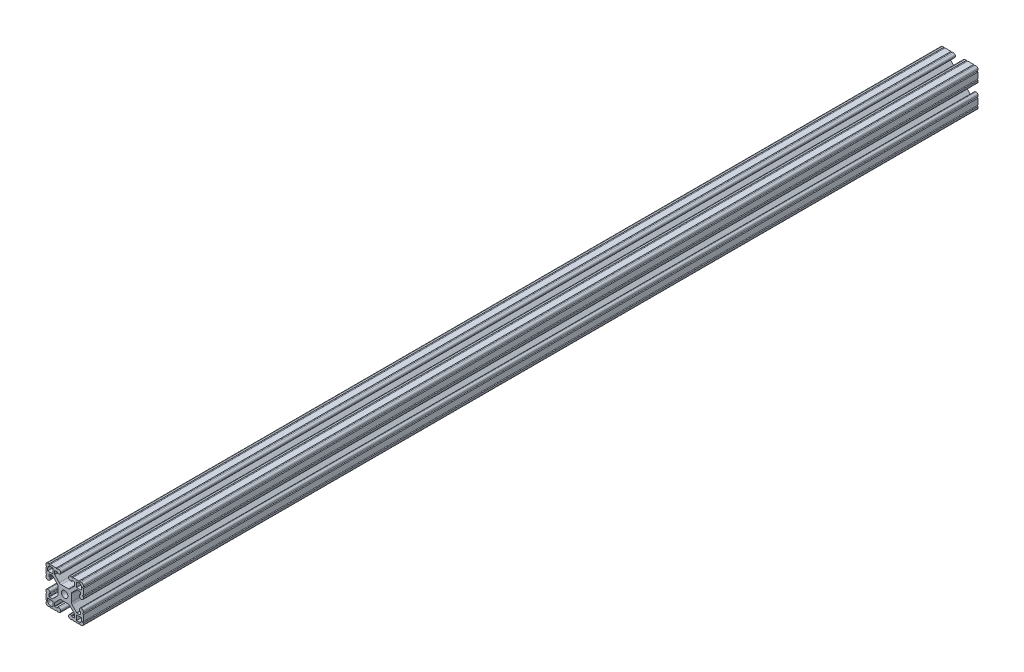
SolidWorks part; units mm, degrees
ref_plane "Front Plane" through (0, 0, 0) normal (0, 0, 1) x (1, 0, 0)
ref_plane "Top Plane" through (0, 0, 0) normal (0, 1, 0) x (1, 0, 0)
ref_plane "Right Plane" through (0, 0, 0) normal (1, 0, 0) x (0, 0, -1)
sketch "Sketch1" plane through (0, 0, 0) normal (0, 0, 1) x (1, 0, 0)
  line L0 (0, -19.05) -> (0, 19.05) construction
  line L1 (19.05, 0) -> (-19.05, 0) construction
  line L2 (4.064, 19.05) -> (-4.064, 19.05) construction
  line L3 (0, -6.7564) -> (0, 6.7564) construction
  line L4 (-4.064, 19.05) -> (-4.064, 14.986) construction
  line L5 (19.05, -10.287) -> (19.05, 10.287) construction
  line L6 (0, -3.3274) -> (0, 3.3274) construction
  line L7 (0, 0) -> (-19.05, 19.05) construction
  line L8 (-8.4474, 10.6026) -> (-10.6026, 8.4474) construction
  point P4 (0, 0)
  point P8 (0, 0)
  point P11 (0, 19.05)
  point P14 (0, 0)
  point P18 (19.05, 0)
  point P21 (0, 0)
  point P24 (-9.525, 9.525)
  point P26 (-9.525, 9.525)
  dimension "T-Slot Width" = 8.128
  dimension "Thickness" = 4.064
  dimension "Opening Width" = 20.574
  dimension "Slot Depth" = 12.2936
  dimension "Center Hole Diameter" = 6.6548
  dimension "Rail Height" = 38.1
  dimension "Rail Width" = 38.1
  dimension "D1" = 45
  dimension "Wall" = 3.048
sketch "Sketch2" plane through (0, 0, 0) normal (1, 0, 0) x (0, 0, -1)
  line L0 (-457.2, 0) -> (457.2, 0) construction
  line L1 (-381, -19.05) -> (-381, 19.05) construction
  line L2 (381, -19.05) -> (381, 19.05) construction
  line L3 (0, -19.05) -> (0, 19.05) construction
  point P4 (0, 0)
  point P7 (-381, 0)
  point P10 (381, 0)
  dimension "Length" = 914.4
  dimension "D1" = 76.2
  dimension "D2" = 76.2
sketch "Sketch3" plane through (0, 0, 0) normal (0, 0, 1) x (1, 0, 0)
  line L1 (19.05, -19.05) -> (-19.05, -19.05)
  line L2 (19.05, -19.05) -> (19.05, 19.05)
  line L3 (19.05, 19.05) -> (-19.05, 19.05)
  line L4 (-19.05, -19.05) -> (-19.05, 19.05)
  line L5 (19.05, -19.05) -> (-19.05, 19.05) construction
  line L6 (19.05, 19.05) -> (-19.05, -19.05) construction
  point P0 (0, 0)
extrude "Boss-Extrude1" add sketch "Sketch3" along normal up to vertex (457.2 mm away) and the other way up to vertex (457.2 mm away) up to point (0, 0, 457.2) other way up to point (0, 0, -457.2)
sketch "Sketch4" plane through (0, 0, 457.2) normal (0, 0, 1) x (1, 0, 0)
  line L4 (4.064, 14.986) -> (4.064, 19.05)
  line L5 (7.239, 14.986) -> (4.064, 14.986)
  line L6 (19.05, 0) -> (-19.05, 0) construction
  line L7 (4.6011, 6.7564) -> (-4.6011, 6.7564)
  line L8 (-4.6011, 6.7564) -> (-10.287, 12.4423)
  line L37 (-19.05, 19.05) -> (-19.05, -19.05) construction
  line L38 (-19.05, -19.05) -> (19.05, -19.05) construction
  line L39 (-10.287, 12.4423) -> (-10.287, 16.002)
  line L40 (-10.287, 16.002) -> (-7.239, 16.002)
  line L41 (-7.239, 16.002) -> (-7.239, 14.986)
  line L42 (-7.239, 14.986) -> (-4.064, 14.986)
  line L43 (-4.064, 14.986) -> (-4.064, 19.05)
  line L44 (-4.064, 19.05) -> (4.064, 19.05)
  line L45 (0, 19.05) -> (0, 0) construction
  line L46 (-19.05, 19.05) -> (0, 0) construction
  line L47 (7.239, 16.002) -> (7.239, 14.986)
  line L48 (10.287, 16.002) -> (7.239, 16.002)
  line L49 (10.287, 12.4423) -> (10.287, 16.002)
  line L50 (4.6011, 6.7564) -> (10.287, 12.4423)
  line L51 (-19.05, 0) -> (19.05, 0) construction
  line L52 (4.6011, -6.7564) -> (10.287, -12.4423)
  line L53 (10.287, -12.4423) -> (10.287, -16.002)
  line L54 (10.287, -16.002) -> (7.239, -16.002)
  line L55 (7.239, -16.002) -> (7.239, -14.986)
  line L56 (-4.064, -19.05) -> (4.064, -19.05)
  line L57 (-4.064, -14.986) -> (-4.064, -19.05)
  line L58 (-7.239, -14.986) -> (-4.064, -14.986)
  line L59 (-7.239, -16.002) -> (-7.239, -14.986)
  line L60 (-10.287, -16.002) -> (-7.239, -16.002)
  line L61 (-10.287, -12.4423) -> (-10.287, -16.002)
  line L62 (-4.6011, -6.7564) -> (-10.287, -12.4423)
  line L63 (4.6011, -6.7564) -> (-4.6011, -6.7564)
  line L64 (7.239, -14.986) -> (4.064, -14.986)
  line L65 (4.064, -14.986) -> (4.064, -19.05)
  line L66 (-6.7564, -4.6011) -> (-12.4423, -10.287)
  line L67 (-12.4423, -10.287) -> (-16.002, -10.287)
  line L68 (-16.002, -10.287) -> (-16.002, -7.239)
  line L69 (-16.002, -7.239) -> (-14.986, -7.239)
  line L70 (-19.05, 4.064) -> (-19.05, -4.064)
  line L71 (-14.986, 4.064) -> (-19.05, 4.064)
  line L72 (-14.986, 7.239) -> (-14.986, 4.064)
  line L73 (-16.002, 7.239) -> (-14.986, 7.239)
  line L74 (-16.002, 10.287) -> (-16.002, 7.239)
  line L75 (-12.4423, 10.287) -> (-16.002, 10.287)
  line L76 (-6.7564, 4.6011) -> (-12.4423, 10.287)
  line L77 (-6.7564, -4.6011) -> (-6.7564, 4.6011)
  line L78 (-14.986, -7.239) -> (-14.986, -4.064)
  line L79 (-14.986, -4.064) -> (-19.05, -4.064)
  line L80 (14.986, -4.064) -> (19.05, -4.064)
  line L81 (14.986, -7.239) -> (14.986, -4.064)
  line L82 (6.7564, -4.6011) -> (6.7564, 4.6011)
  line L83 (6.7564, 4.6011) -> (12.4423, 10.287)
  line L84 (12.4423, 10.287) -> (16.002, 10.287)
  line L85 (16.002, 10.287) -> (16.002, 7.239)
  line L86 (16.002, 7.239) -> (14.986, 7.239)
  line L87 (14.986, 7.239) -> (14.986, 4.064)
  line L88 (14.986, 4.064) -> (19.05, 4.064)
  line L89 (19.05, 4.064) -> (19.05, -4.064)
  line L90 (16.002, -7.239) -> (14.986, -7.239)
  line L91 (16.002, -10.287) -> (16.002, -7.239)
  line L92 (12.4423, -10.287) -> (16.002, -10.287)
  line L93 (6.7564, -4.6011) -> (12.4423, -10.287)
  line L94 (19.05, -19.05) -> (19.05, 19.05) construction
  line L95 (12.065, 17.272) -> (17.272, 17.272)
  line L96 (12.065, 17.272) -> (12.065, 12.065)
  line L97 (12.065, 12.065) -> (17.272, 12.065)
  line L98 (17.272, 17.272) -> (17.272, 12.065)
  line L99 (19.05, 19.05) -> (-19.05, 19.05) construction
  line L100 (17.272, -17.272) -> (17.272, -12.065)
  line L101 (12.065, -17.272) -> (17.272, -17.272)
  line L102 (12.065, -17.272) -> (12.065, -12.065)
  line L103 (12.065, -12.065) -> (17.272, -12.065)
  line L104 (-17.272, 17.272) -> (-17.272, 12.065)
  line L105 (-12.065, 12.065) -> (-17.272, 12.065)
  line L106 (-12.065, 17.272) -> (-12.065, 12.065)
  line L107 (-12.065, 17.272) -> (-17.272, 17.272)
  line L108 (-12.065, -12.065) -> (-17.272, -12.065)
  line L109 (-12.065, -17.272) -> (-12.065, -12.065)
  line L110 (-12.065, -17.272) -> (-17.272, -17.272)
  line L111 (-17.272, -17.272) -> (-17.272, -12.065)
  circle A5 centre (0, 0) radius 3.3274
  point P21 (0, 6.7564)
  point P23 (0, -6.7564)
  point P38 (-6.7564, 0)
  point P53 (6.7564, 0)
  dimension "D1" = 20.574
  dimension "D3" = 3.048
  dimension "D4" = 3.048
  dimension "D5" = 1.778
  dimension "D6" = 1.778
  dimension "D7" = 1.778
extrude "Cut-Extrude1" cut sketch "Sketch4" against normal through all
sketch "Sketch5" plane through (0, 0, 457.2) normal (0, 0, 1) x (1, 0, 0)
  line L4 (-4.064, 19.05) -> (-19.05, 19.05) construction
  line L26 (-19.05, 19.05) -> (-19.05, 4.064) construction
  line L27 (-15.875, 19.05) -> (-14.605, 19.05)
  line L28 (-8.509, 19.05) -> (-7.239, 19.05)
  line L29 (-19.05, 15.875) -> (-19.05, 14.605)
  line L30 (-19.05, 8.509) -> (-19.05, 7.239)
  line L31 (8.509, 19.05) -> (7.239, 19.05)
  line L32 (15.875, 19.05) -> (14.605, 19.05)
  line L33 (19.05, 15.875) -> (19.05, 14.605)
  line L34 (19.05, 8.509) -> (19.05, 7.239)
  line L35 (19.05, -8.509) -> (19.05, -7.239)
  line L36 (19.05, -15.875) -> (19.05, -14.605)
  line L37 (15.875, -19.05) -> (14.605, -19.05)
  line L38 (8.509, -19.05) -> (7.239, -19.05)
  line L39 (-8.509, -19.05) -> (-7.239, -19.05)
  line L40 (-15.875, -19.05) -> (-14.605, -19.05)
  line L41 (-19.05, -15.875) -> (-19.05, -14.605)
  line L42 (-19.05, -8.509) -> (-19.05, -7.239)
  line L43 (19.05, 19.05) -> (4.064, 19.05) construction
  line L44 (19.05, 4.064) -> (19.05, 19.05) construction
  line L48 (-14.986, 4.064) -> (-19.05, 4.064) construction
  line L49 (-4.064, 14.986) -> (-4.064, 19.05) construction
  arc A8 (-15.875, 19.05) -> (-14.605, 19.05) centre (-15.24, 19.05) ccw
  arc A9 (-8.509, 19.05) -> (-7.239, 19.05) centre (-7.874, 19.05) ccw
  arc A10 (-19.05, 14.605) -> (-19.05, 15.875) centre (-19.05, 15.24) ccw
  arc A11 (-19.05, 7.239) -> (-19.05, 8.509) centre (-19.05, 7.874) ccw
  arc A12 (7.239, 19.05) -> (8.509, 19.05) centre (7.874, 19.05) ccw
  arc A13 (14.605, 19.05) -> (15.875, 19.05) centre (15.24, 19.05) ccw
  arc A14 (19.05, 15.875) -> (19.05, 14.605) centre (19.05, 15.24) ccw
  arc A15 (19.05, 8.509) -> (19.05, 7.239) centre (19.05, 7.874) ccw
  arc A16 (19.05, -7.239) -> (19.05, -8.509) centre (19.05, -7.874) ccw
  arc A17 (19.05, -14.605) -> (19.05, -15.875) centre (19.05, -15.24) ccw
  arc A18 (15.875, -19.05) -> (14.605, -19.05) centre (15.24, -19.05) ccw
  arc A19 (8.509, -19.05) -> (7.239, -19.05) centre (7.874, -19.05) ccw
  arc A20 (-7.239, -19.05) -> (-8.509, -19.05) centre (-7.874, -19.05) ccw
  arc A21 (-14.605, -19.05) -> (-15.875, -19.05) centre (-15.24, -19.05) ccw
  arc A22 (-19.05, -15.875) -> (-19.05, -14.605) centre (-19.05, -15.24) ccw
  arc A23 (-19.05, -8.509) -> (-19.05, -7.239) centre (-19.05, -7.874) ccw
  dimension "D2" = 0.635
  dimension "D4" = 3.81
  dimension "D5" = 3.81
  dimension "D1" = 3.81
  dimension "D3" = 3.81
  dimension "D7" = 4
extrude "Cut-Extrude2" cut sketch "Sketch5" against normal through all
fillet "Fillet1" radius 2.54 12 edges at (-6.7564, 4.6011, 0) (-6.7564, -4.6011, 0) (4.6011, -6.7564, 0) (-4.6011, -6.7564, 0) (6.7564, -4.6011, 0) (6.7564, 4.6011, 0) (4.6011, 6.7564, 0) (-4.6011, 6.7564, 0) (-17.272, 17.272, 0) (17.272, 17.272, 0) (17.272, -17.272, 0) (-17.272, -17.272, 0)
fillet "Fillet2" radius 1.778 20 edges at (19.05, -19.05, 0) (19.05, 19.05, 0) (-19.05, -19.05, 0) (-19.05, 19.05, 0) (-14.986, 4.064, 0) (-19.05, 4.064, 0) (-19.05, -4.064, 0) (-14.986, -4.064, 0) (-4.064, -19.05, 0) (-4.064, -14.986, 0) (4.064, -14.986, 0) (4.064, -19.05, 0) (19.05, -4.064, 0) (14.986, -4.064, 0) (19.05, 4.064, 0) (14.986, 4.064, 0) (4.064, 14.986, 0) (4.064, 19.05, 0) (-4.064, 19.05, 0) (-4.064, 14.986, 0)
fillet "Fillet3" radius 0.3969 24 edges at (-14.986, -7.239, 0) (-16.002, -10.287, 0) (-12.4423, -10.287, 0) (-12.4423, 10.287, 0) (-16.002, 7.239, 0) (-16.002, 10.287, 0) (-10.287, 12.4423, 0) (-7.239, 16.002, 0) (-10.287, 16.002, 0) (10.287, 16.002, 0) (7.239, 16.002, 0) (10.287, 12.4423, 0) (16.002, 10.287, 0) (12.4423, 10.287, 0) (16.002, 7.239, 0) (16.002, -7.239, 0) (16.002, -10.287, 0) (12.4423, -10.287, 0) (10.287, -12.4423, 0) (10.287, -16.002, 0) (7.239, -16.002, 0) (-7.239, -16.002, 0) (-10.287, -12.4423, 0) (-10.287, -16.002, 0)
equation "\"D4@Sketch5\"=\"D3@Sketch5\""
equation "\"D5@Sketch5\"=\"D4@Sketch5\""
equation "\"D1@Sketch4\"=\"Opening Width@Sketch1\""
equation "\"D2@Sketch2\"=\"D1@Sketch2\""
